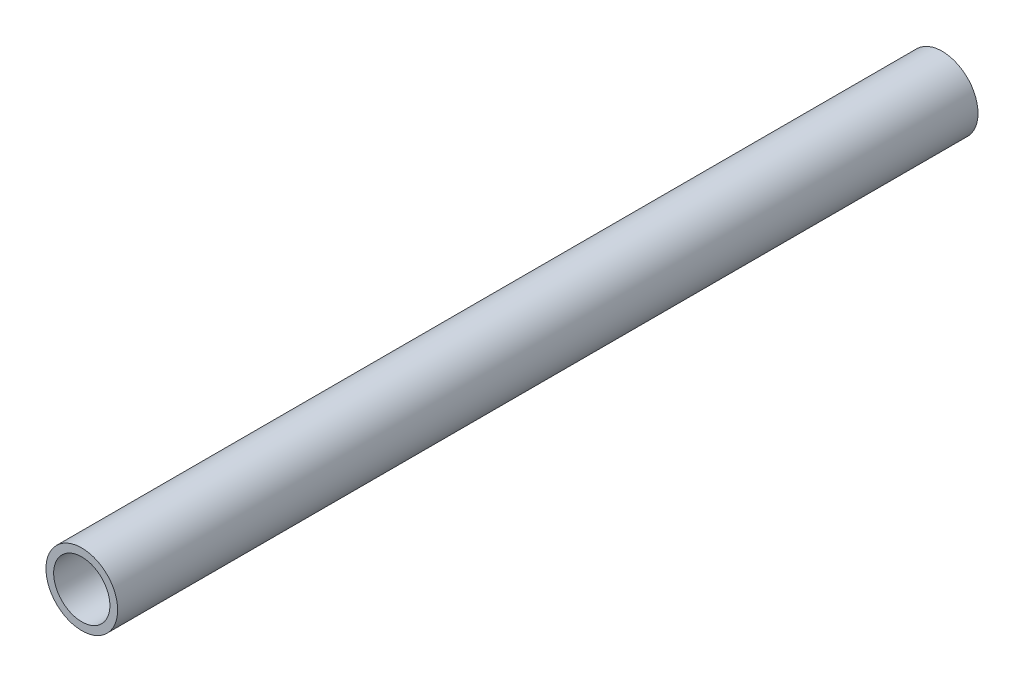
SolidWorks part; units mm, degrees
ref_plane "Front Plane" through (0, 0, 0) normal (0, 0, 1) x (1, 0, 0)
ref_plane "Top Plane" through (0, 0, 0) normal (0, 1, 0) x (1, 0, 0)
ref_plane "Right Plane" through (0, 0, 0) normal (1, 0, 0) x (0, 0, -1)
sketch "Sketch1" plane through (0, 0, 0) normal (0, 0, 1) x (1, 0, 0)
  circle A0 centre (0, 0) radius 13.335
  dimension "Pipe OD" = 26.67
extrude "Extrude-Thin1" add sketch "Sketch1" along normal mid plane 320 thin thin type one direction reverse wall 2.8702
